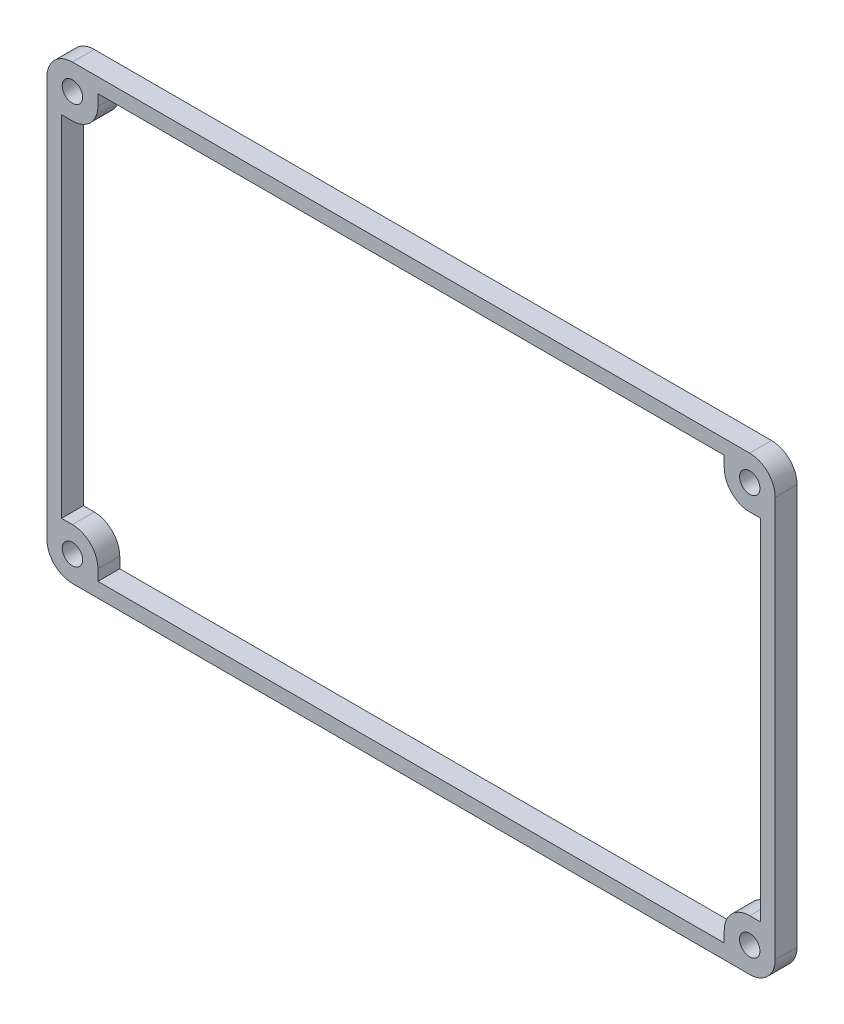
SolidWorks part; units mm, degrees
ref_plane "Front Plane" through (0, 0, 0) normal (0, 0, 1) x (1, 0, 0)
ref_plane "Top Plane" through (0, 0, 0) normal (0, 1, 0) x (1, 0, 0)
ref_plane "Right Plane" through (0, 0, 0) normal (1, 0, 0) x (0, 0, -1)
sketch "Sketch1" plane through (0, 0, 0) normal (0, 0, 1) x (1, 0, 0)
  line L1 (-46.5, -31) -> (46.5, -31)
  line L2 (-50, -27.5) -> (-50, 27.5)
  line L3 (-46.5, 31) -> (46.5, 31)
  line L4 (50, -27.5) -> (50, 27.5)
  line L5 (-50, -31) -> (50, 31) construction
  line L6 (-50, 31) -> (50, -31) construction
  circle A0 centre (-46.5, 27.5) radius 1.4
  circle A1 centre (46.5, 27.5) radius 1.4
  circle A2 centre (46.5, -27.5) radius 1.4
  circle A3 centre (-46.5, -27.5) radius 1.4
  arc A4 (-46.5, -31) -> (-50, -27.5) centre (-46.5, -27.5) cw
  arc A5 (46.5, -31) -> (50, -27.5) centre (46.5, -27.5) ccw
  arc A6 (46.5, 31) -> (50, 27.5) centre (46.5, 27.5) cw
  arc A7 (-50, 27.5) -> (-46.5, 31) centre (-46.5, 27.5) cw
  point P14 (0, 0)
  dimension "D1" = 2.8
  dimension "D8" = 3.5
  dimension "D2" = 46.5
  dimension "D3" = 46.5
  dimension "D4" = 27.5
  dimension "D5" = 27.5
  dimension "D6" = 100
  dimension "D7" = 62
extrude "Boss-Extrude1" add sketch "Sketch1" along normal blind 3
sketch "Sketch2" plane through (0, 0, 3) normal (0, 0, 1) x (1, 0, 0)
  line L0 (46.5, 31) -> (-46.5, 31) construction
  line L1 (-43, -29) -> (43, -29)
  line L2 (-43, -29) -> (-43, 29)
  line L3 (-43, 29) -> (43, 29)
  line L4 (43, -29) -> (43, 29)
  line L5 (-43, -29) -> (43, 29) construction
  line L6 (-43, 29) -> (43, -29) construction
  line L7 (-48, -24) -> (48, -24)
  line L8 (-48, -24) -> (-48, 24)
  line L9 (-48, 24) -> (48, 24)
  line L10 (48, -24) -> (48, 24)
  line L11 (-48, -24) -> (48, 24) construction
  line L12 (-48, 24) -> (48, -24) construction
  line L13 (50, -27.5) -> (50, 27.5) construction
  point P0 (0, 0)
  point P6 (0, 0)
  dimension "D1" = 2
  dimension "D2" = 2
  dimension "D3" = 7
  dimension "D4" = 7
extrude "Cut-Extrude1" cut sketch "Sketch2" against normal blind 3 contours L9 L8 L7 L2 | L9 L2 L7 L4 | L2 L9 L4 L3 | L7 L10 L9 L4 | L7 L2 L1 L4
fillet "Fillet1" radius 3.5 4 edges at (-43, -24, 1.5) (43, -24, 1.5) (43, 24, 1.5) (-43, 24, 1.5)
